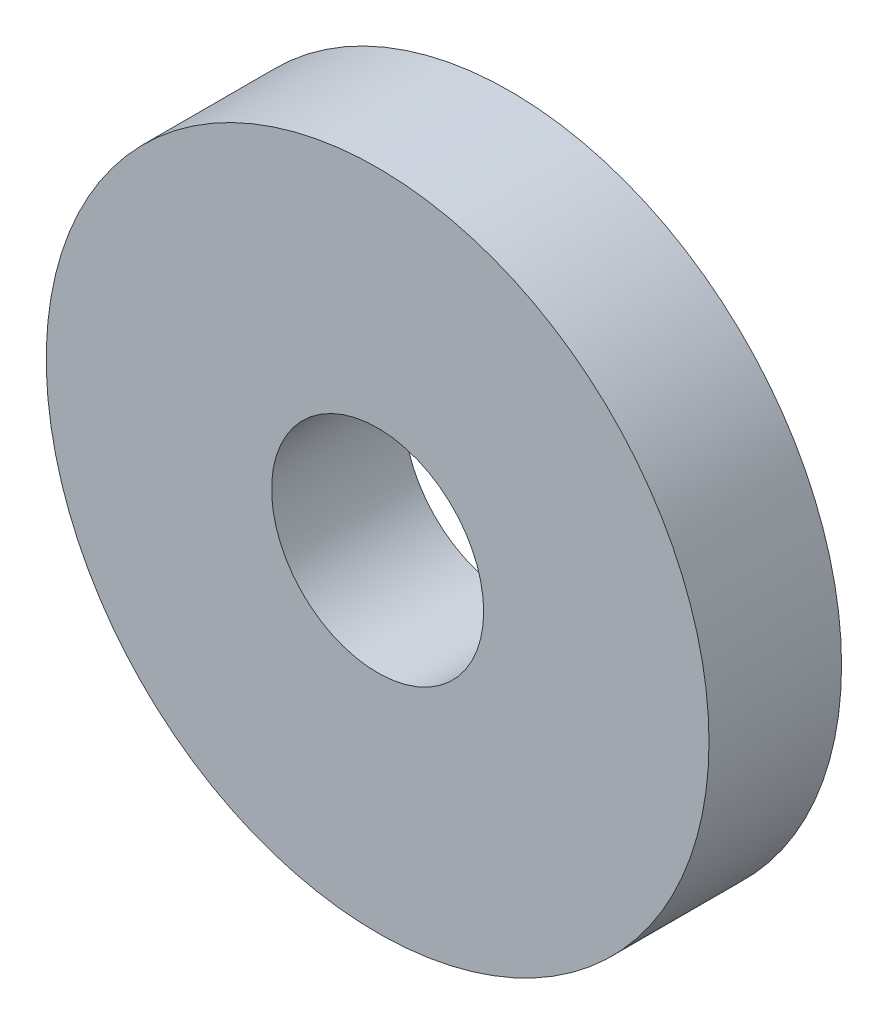
SolidWorks part; units mm, degrees
material "Thornel Mat VMA"
ref_plane "前视基准面" through (0, 0, 0) normal (0, 0, 1) x (1, 0, 0)
ref_plane "上视基准面" through (0, 0, 0) normal (0, 1, 0) x (1, 0, 0)
ref_plane "右视基准面" through (0, 0, 0) normal (1, 0, 0) x (0, 0, -1)
sketch "草图1" plane through (0, 0, 0) normal (0, 0, 1) x (1, 0, 0)
  circle A0 centre (0, 0) radius 1.6
  circle A1 centre (0, 0) radius 5
  dimension "D1" = 3.2
  dimension "D2" = 10
extrude "凸台-拉伸1" add sketch "草图1" along normal blind 2
